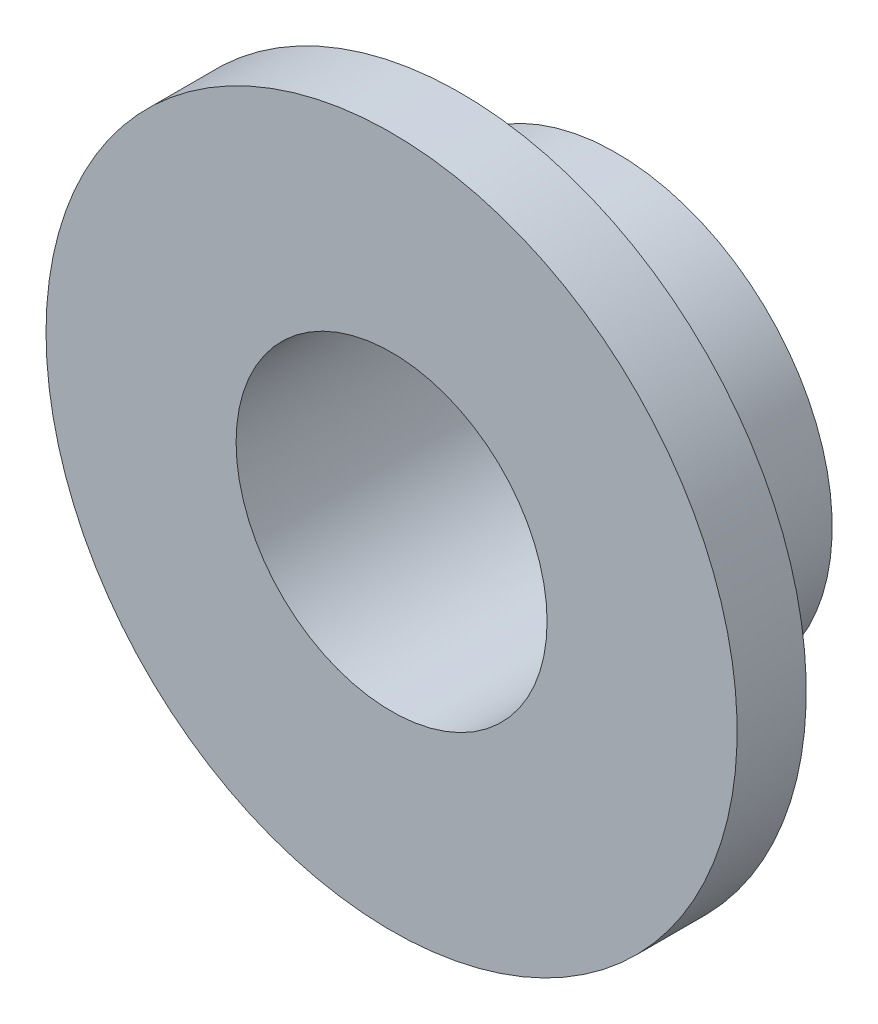
SolidWorks part; units mm, degrees
material "AISI 1020"
ref_plane "Спереди" through (0, 0, 0) normal (0, 0, 1) x (1, 0, 0)
ref_plane "Сверху" through (0, 0, 0) normal (0, 1, 0) x (1, 0, 0)
ref_plane "Справа" through (0, 0, 0) normal (1, 0, 0) x (0, 0, -1)
sketch "Эскиз1" plane through (0, 0, 0) normal (1, 0, 0) x (0, 0, -1)
  line L0 (8, 0) -> (-10, 0) construction
  line L1 (-10, 4.5) -> (-10, -4.5) construction
  line L2 (4, 4.5) -> (4, 6.25)
  line L3 (4, 13.5) -> (4, -15.188) construction
  line L4 (4, 6.25) -> (-0.5, 6.25)
  line L5 (-0.5, 6.25) -> (-0.5, 10)
  line L6 (-0.5, 10) -> (-2.5, 10)
  line L7 (-2.5, 10) -> (-2.5, 4.5)
  line L8 (-2.5, 4.5) -> (4, 4.5)
  line L9 (4, 6.5) -> (0, 6.5) construction
  line L10 (0, 13.5) -> (0, -15.188) construction
  dimension "D1" = 0.25
  dimension "D2" = 0.5
  dimension "D3" = 2
  dimension "D4" = 20
  dimension "D5" = 9
revolve "Повернуть1" add sketch "Эскиз1" angle 360 about L0
